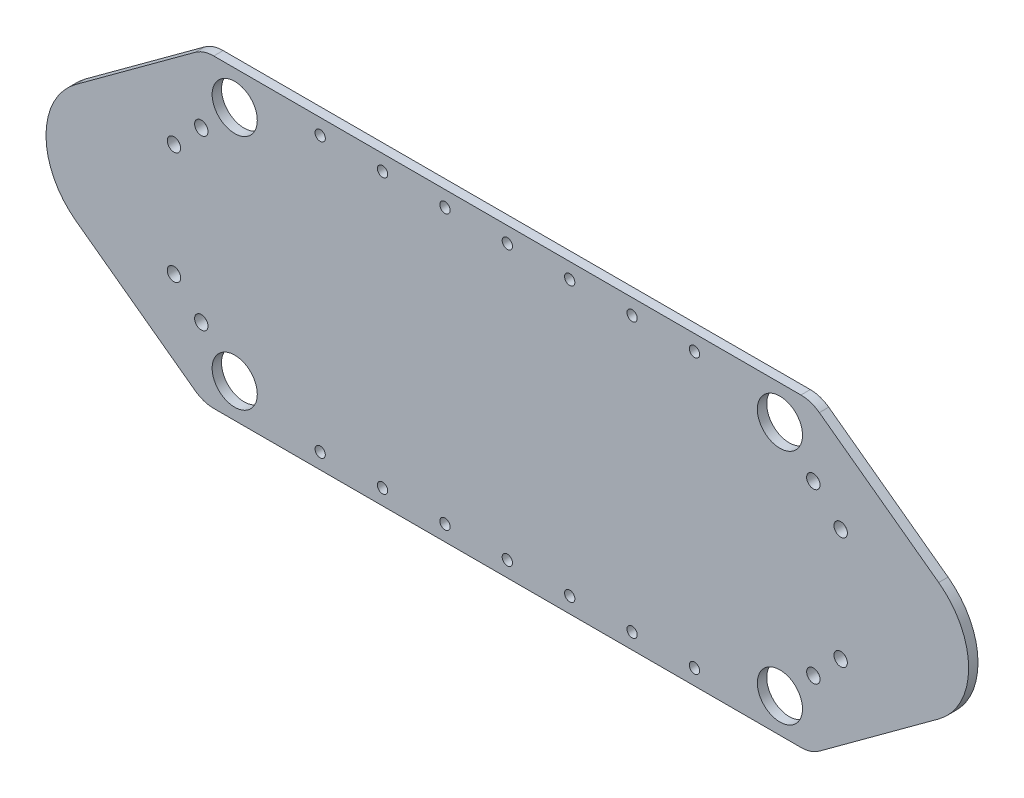
SolidWorks part; units mm, degrees
material "Thornel Mat VMA"
ref_plane "Front Plane" through (0, 0, 0) normal (0, 0, 1) x (1, 0, 0)
ref_plane "Top Plane" through (0, 0, 0) normal (0, 1, 0) x (1, 0, 0)
ref_plane "Right Plane" through (0, 0, 0) normal (1, 0, 0) x (0, 0, -1)
sketch "Sketch1" plane through (0, 0, 0) normal (0, 0, 1) x (1, 0, 0)
  line L0 (-87.4, 38) -> (87.4, 38) construction
  line L1 (0, 38) -> (0, -38) construction
  line L2 (-87.4, 48.9336) -> (87.4, 48.9336)
  line L3 (-87.4, 48.9336) -> (-97.4, 48.9336)
  line L4 (-97.4, 48.9336) -> (-138.2946, 18.9523)
  line L5 (-124.4, 0) -> (0, 0) construction
  line L6 (-97.4, -48.9336) -> (-138.2946, -18.9523)
  line L7 (-87.4, -48.9336) -> (-97.4, -48.9336)
  line L8 (-87.4, -48.9336) -> (87.4, -48.9336)
  line L9 (87.4, -48.9336) -> (97.4, -48.9336)
  line L10 (97.4, -48.9336) -> (138.2946, -18.9523)
  line L11 (97.4, 48.9336) -> (138.2946, 18.9523)
  line L12 (87.4, 48.9336) -> (97.4, 48.9336)
  circle A0 centre (-87.4, -38) radius 7.239
  circle A1 centre (-87.4, 38) radius 7.239
  circle A2 centre (87.4, -38) radius 7.239
  circle A3 centre (87.4, 38) radius 7.239
  circle A4 centre (98.1105, -27) radius 2.15
  circle A5 centre (106.8737, -18) radius 2.15
  circle A6 centre (106.8737, 18) radius 2.15
  circle A7 centre (98.1105, 27) radius 2.15
  circle A8 centre (-98.1105, -27) radius 2.15
  circle A9 centre (-106.8737, -18) radius 2.15
  circle A10 centre (-106.8737, 18) radius 2.15
  circle A11 centre (-98.1105, 27) radius 2.15
  circle A12 centre (-60, -43.9336) radius 1.65
  arc A13 (-138.2946, 18.9523) -> (-138.2946, -18.9523) centre (-124.4, 0) ccw
  arc A14 (138.2946, 18.9523) -> (138.2946, -18.9523) centre (124.4, 0) cw
  circle A15 centre (0, 43.9336) radius 1.65
  circle A16 centre (20, 43.9336) radius 1.65
  circle A17 centre (40, 43.9336) radius 1.65
  circle A18 centre (60, 43.9336) radius 1.65
  circle A19 centre (-20, 43.9336) radius 1.65
  circle A20 centre (-40, 43.9336) radius 1.65
  circle A21 centre (-60, 43.9336) radius 1.65
  circle A22 centre (-40, -43.9336) radius 1.65
  circle A23 centre (-20, -43.9336) radius 1.65
  circle A24 centre (0, -43.9336) radius 1.65
  circle A25 centre (20, -43.9336) radius 1.65
  circle A26 centre (40, -43.9336) radius 1.65
  circle A27 centre (60, -43.9336) radius 1.65
  point P43 (0, -48.9336)
  point P49 (0, 48.9336)
  dimension "D1" = 3.3
  dimension "D2" = 5
  dimension "D5" = 20
  dimension "D6" = 20
  dimension "D3" = 4
  dimension "D4" = 4
extrude "Boss-Extrude1" add sketch "Sketch1" along normal blind 3
fillet "Fillet1" radius 10 4 edges at (97.4, -48.9336, 1.5) (-97.4, -48.9336, 1.5) (97.4, 48.9336, 1.5) (-97.4, 48.9336, 1.5)
sketch "Sketch2" plane through (0, 0, 3) normal (0, 0, 1) x (1, 0, 0)
  point P0 (0, 0)
